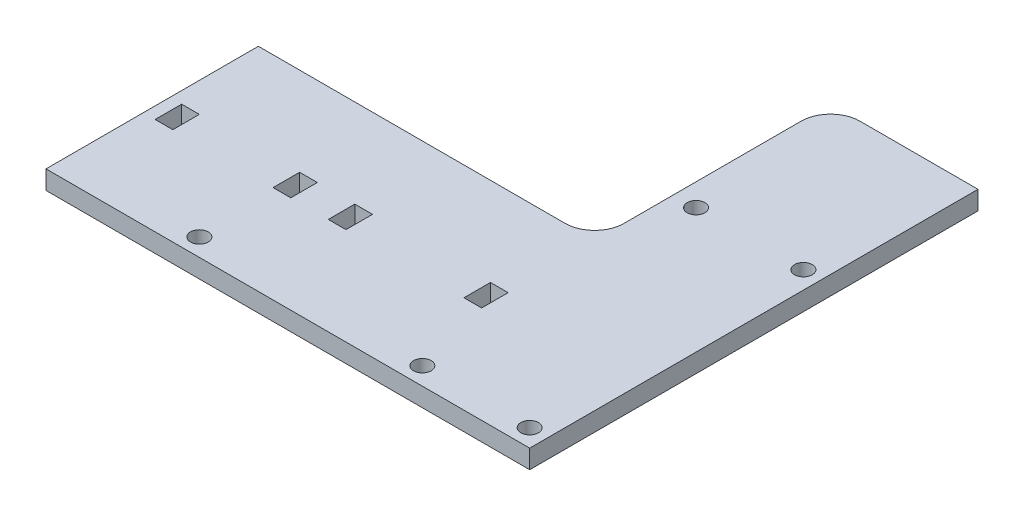
SolidWorks part; units mm, degrees
ref_plane "Front Plane" through (0, 0, 0) normal (0, 0, 1) x (1, 0, 0)
ref_plane "Top Plane" through (0, 0, 0) normal (0, 1, 0) x (1, 0, 0)
ref_plane "Right Plane" through (0, 0, 0) normal (1, 0, 0) x (0, 0, -1)
sketch "Sketch1" plane through (0, 0, 0) normal (0, 1, 0) x (1, 0, 0)
  line L1 (0, 0) -> (82, 0)
  line L2 (0, 0) -> (0, -36)
  line L3 (0, -36) -> (82, -36)
  line L4 (82, 0) -> (82, -36)
  line L5 (82, 0) -> (57, 0)
  line L6 (82, 0) -> (82, 40)
  line L7 (82, 40) -> (57, 40)
  line L8 (57, 0) -> (57, 40)
  dimension "D1" = 82
  dimension "D2" = 36
  dimension "D3" = 40
  dimension "D4" = 25
extrude "Boss-Extrude1" add sketch "Sketch1" along normal blind 3.175 contours L8 L1 L6 L7 | L4 L1 L2 L3
sketch "Sketch2" plane through (0, 3.175, 0) normal (0, 1, 0) x (1, 0, 0)
  line L0 (82, -36) -> (82, 40) construction
  line L3 (0, -36) -> (82, -36) construction
  line L4 (31.35, -15) -> (34.35, -15)
  line L5 (54.35, -15) -> (57.35, -15)
  line L6 (54.35, -15) -> (54.35, -19.5)
  line L7 (54.35, -19.5) -> (57.35, -19.5)
  line L8 (57.35, -15) -> (57.35, -19.5)
  line L9 (31.35, -15) -> (31.35, -19.5)
  line L10 (31.35, -19.5) -> (34.35, -19.5)
  line L11 (34.35, -15) -> (34.35, -19.5)
  line L12 (0, 0) -> (0, -36) construction
  line L13 (5, -19.5) -> (2, -19.5)
  line L14 (5, -19.5) -> (5, -15)
  line L15 (5, -15) -> (2, -15)
  line L16 (2, -19.5) -> (2, -15)
  line L17 (25, -19.5) -> (22, -19.5)
  line L18 (25, -19.5) -> (25, -15)
  line L19 (25, -15) -> (22, -15)
  line L22 (-14.65, -15) -> (-11.65, -15) [skipped]
  line L23 (-14.65, -15) -> (-14.65, -19.5) [skipped]
  line L24 (-14.65, -19.5) -> (-11.65, -19.5) [skipped]
  line L25 (-11.65, -15) -> (-11.65, -19.5) [skipped]
  line L26 (8.35, -15) -> (11.35, -15) [skipped]
  line L27 (8.35, -15) -> (8.35, -19.5) [skipped]
  line L28 (8.35, -19.5) -> (11.35, -19.5) [skipped]
  line L29 (11.35, -15) -> (11.35, -19.5) [skipped]
  line L30 (22, -19.5) -> (22, -15)
  circle A0 centre (79, -33) radius 1.5
  circle A1 centre (60.8, -33) radius 1.5
  circle A2 centre (60.8, 13.4) radius 1.5
  circle A3 centre (79, 13.4) radius 1.5
  circle A4 centre (23, -33) radius 1.5
  point P0 (79, -33)
  point P1 (57, -33)
  point P5 (23, -33)
  point P14 (54.35, -15)
  point P23 (-14.65, -15)
  point P24 (31.35, -15)
  point P30 (8.35, -15)
  dimension "D3" = 3
  dimension "D8" = 3
  dimension "D1" = 3
  dimension "D2" = 3
  dimension "D6" = 25
  dimension "D7" = 34
  dimension "D9" = 27.65
  dimension "D10" = 21
  dimension "D11" = 3
  dimension "D12" = 4.5
  dimension "D14" = 20
  dimension "D15" = 3
  dimension "D16" = 2
  dimension "D4" = 2
  dimension "D5" = 2
  dimension "D13" = 4
  dimension "D17" = 2
extrude "Cut-Extrude1" cut sketch "Sketch2" against normal up to next
fillet "Fillet1" radius 5 2 edges at (57, 1.5875, -40) (57, 1.5875, 0)
